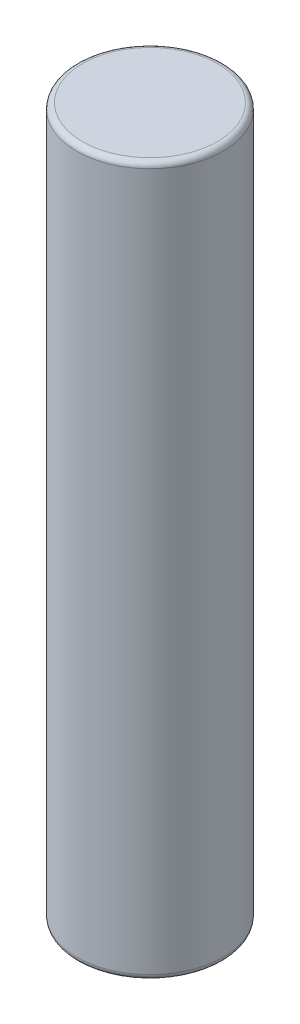
SolidWorks part; units mm, degrees
ref_plane "Front Plane" through (0, 0, 0) normal (0, 0, 1) x (1, 0, 0)
ref_plane "Top Plane" through (0, 0, 0) normal (0, 1, 0) x (1, 0, 0)
ref_plane "Right Plane" through (0, 0, 0) normal (1, 0, 0) x (0, 0, -1)
sketch "Sketch1" plane through (0, 0, 0) normal (0, 1, 0) x (1, 0, 0)
  circle A0 centre (0, 0) radius 6.5
  dimension "D1" = 13
extrude "Boss-Extrude1" add sketch "Sketch1" along normal blind 63
fillet "Fillet1" radius 0.5 2 edges at (0, 0, 6.5) (0, 63, 6.5)
